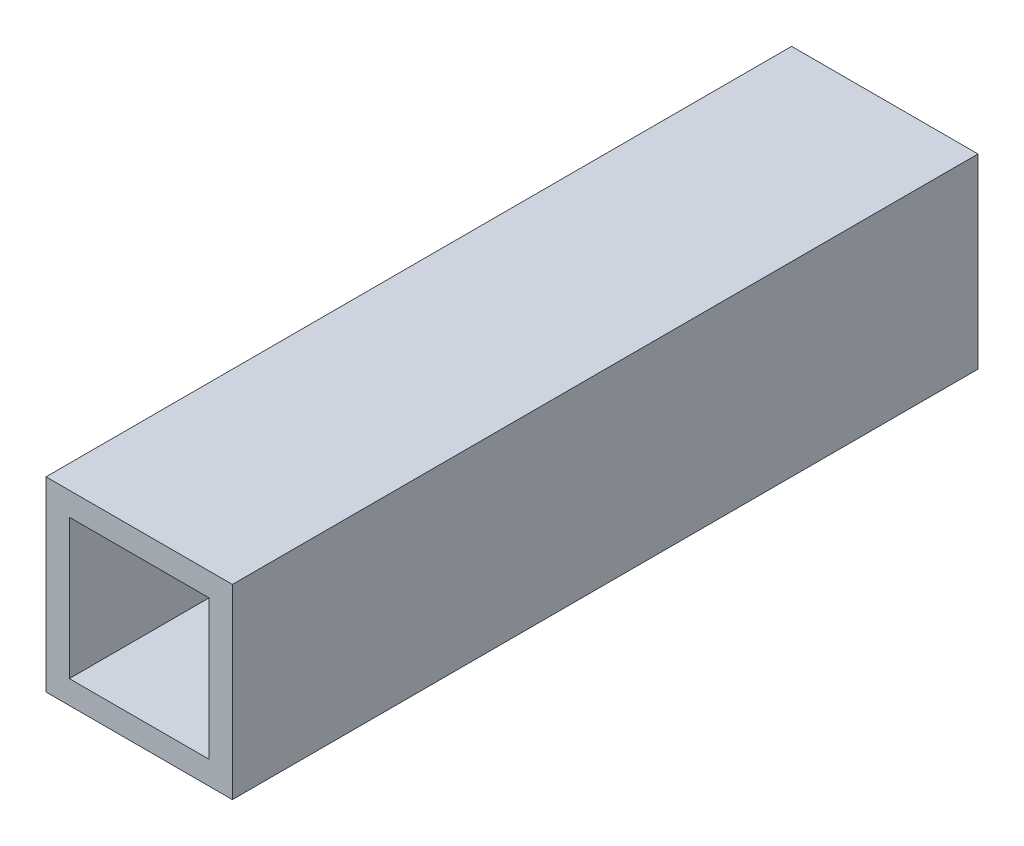
SolidWorks part; units mm, degrees
material "6061-T6 (SS)"
ref_plane "Front Plane" through (0, 0, 0) normal (0, 0, 1) x (1, 0, 0)
ref_plane "Top Plane" through (0, 0, 0) normal (0, 1, 0) x (1, 0, 0)
ref_plane "Right Plane" through (0, 0, 0) normal (1, 0, 0) x (0, 0, -1)
sketch "Sketch1" plane through (0, 0, 0) normal (0, 0, 1) x (1, 0, 0)
  line L0 (-12.7, -12.7) -> (12.7, -12.7)
  line L1 (-12.7, -12.7) -> (-12.7, 12.7)
  line L2 (12.7, -12.7) -> (12.7, 12.7)
  line L3 (-12.7, 12.7) -> (12.7, 12.7)
  line L4 (-12.7, -12.7) -> (12.7, 12.7) construction
  line L5 (12.7, -12.7) -> (-12.7, 12.7) construction
  line L7 (-9.525, -9.525) -> (9.525, -9.525)
  line L8 (-9.525, -9.525) -> (-9.525, 9.525)
  line L9 (-9.525, 9.525) -> (9.525, 9.525)
  line L10 (9.525, -9.525) -> (9.525, 9.525)
  line L11 (-9.525, -9.525) -> (9.525, 9.525) construction
  line L12 (-9.525, 9.525) -> (9.525, -9.525) construction
  point P0 (0, 0)
  point P1 (0, 0)
  point P11 (10.618, 10.618)
  dimension "D1" = 25.4
  dimension "D2" = 25.4
  dimension "D3" = 3.175
extrude "Boss-Extrude1" add sketch "Sketch1" along normal blind 101.6
